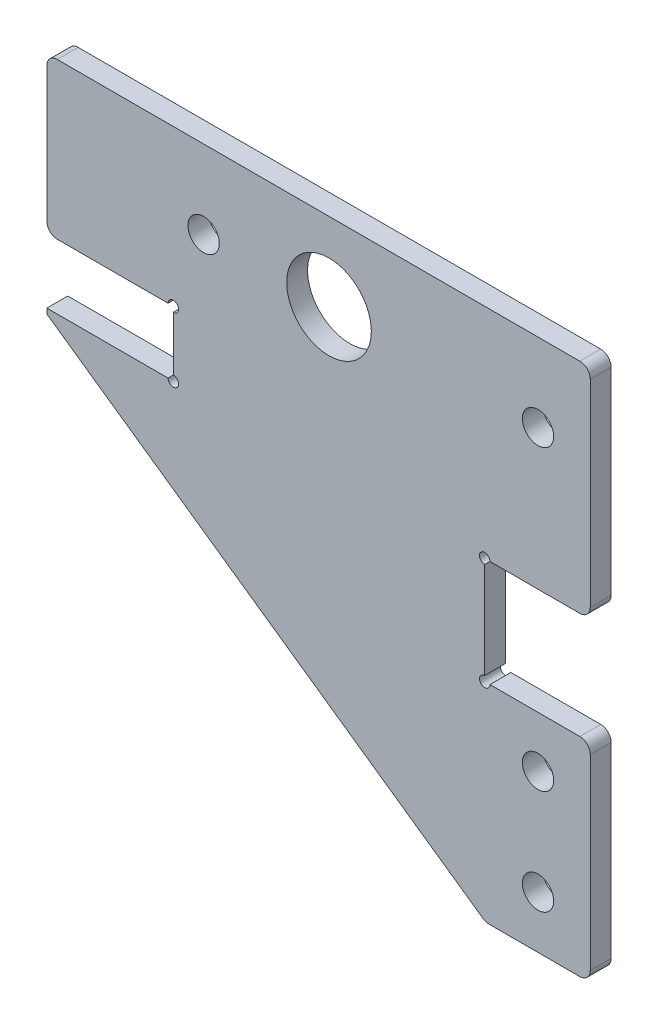
SolidWorks part; units mm, degrees
material "环氧板3240"
ref_plane "前视基准面" through (0, 0, 0) normal (0, 0, 1) x (1, 0, 0)
ref_plane "上视基准面" through (0, 0, 0) normal (0, 1, 0) x (1, 0, 0)
ref_plane "右视基准面" through (0, 0, 0) normal (1, 0, 0) x (0, 0, -1)
other "Configuration Table"
sketch "草图1" plane through (0, 0, 0) normal (0, 0, 1) x (1, 0, 0)
  line L1 (-5, -43.5) -> (5, -43.5)
  line L2 (5, -43.5) -> (5, -23.6)
  line L5 (-47, 7.5) -> (-47, -7.4)
  line L6 (-47, 0) -> (0, 0) construction
  line L7 (0, 0) -> (0, -43.5) construction
  line L10 (5, -23.6) -> (-5.1, -23.6)
  line L11 (-5.1, -23.6) -> (-5.1, -13.4)
  line L13 (-47, -7.4) -> (-34.9, -7.4)
  line L14 (-5.1, -13.4) -> (5, -13.4)
  line L15 (5, -13.4) -> (5, 7.5)
  line L17 (-5, -43.5) -> (-47, -14.0913)
  line L18 (-47, -13.6) -> (-47, -14.0913)
  line L19 (-34.9, -7.4) -> (-34.9, -13.6)
  line L20 (-34.9, -13.6) -> (-47, -13.6)
  line L21 (-47, -13.6) -> (-47, -7.4) construction
  line L22 (-49.5736, -19.2913) -> (-15.2583, -43.3192) construction
  line L23 (-49.5736, -19.2913) -> (-15.2583, -43.3192) construction
  line L27 (5, 7.5) -> (-47, 7.5)
  circle A0 centre (-32, 0) radius 1.5
  circle A1 centre (0, 0) radius 1.5
  circle A2 centre (0, -38.5) radius 1.5
  circle A3 centre (0, -28.5) radius 1.5
  circle A4 centre (-15, 0) radius 1.5 construction
  circle A5 centre (0, -18.5) radius 1.5 construction
  circle A9 centre (-20, 0) radius 4.05
  dimension "D7" = 3
  dimension "D8" = 15
  dimension "D9" = 8.1
  dimension "D10" = 5.1
  dimension "D11" = 10
  dimension "D6" = 15
  dimension "D4" = 10
  dimension "D15" = 20
  dimension "D20" = 145
  dimension "D2" = 10
  dimension "D3" = 52
  dimension "D5" = 7.5
  dimension "D12" = 10.2
  dimension "D13" = 51
  dimension "D14" = 5.1
  dimension "D16" = 14.9
  dimension "D17" = 6.2
  dimension "D18" = 20.9
  dimension "D19" = 39.9
  dimension "D21" = 5
  dimension "D22" = 0.2
extrude "凸台-拉伸1" add sketch "草图1" along normal blind 2
sketch "草图2" plane through (0, 0, 2) normal (0, 0, 1) x (1, 0, 0)
  circle A0 centre (-34.9, -7.4) radius 0.5
  circle A1 centre (-34.9, -13.6) radius 0.5
  circle A2 centre (-5.1, -13.4) radius 0.5
  circle A3 centre (-5.1, -23.6) radius 0.5
  dimension "D1" = 1
extrude "切除-拉伸1" cut sketch "草图2" against normal blind 10
fillet "圆角1" radius 1 7 edges at (-5, -43.5, 1) (5, -43.5, 1) (5, -23.6, 1) (5, -13.4, 1) (5, 7.5, 1) (-47, 7.5, 1) (-47, -7.4, 1)
